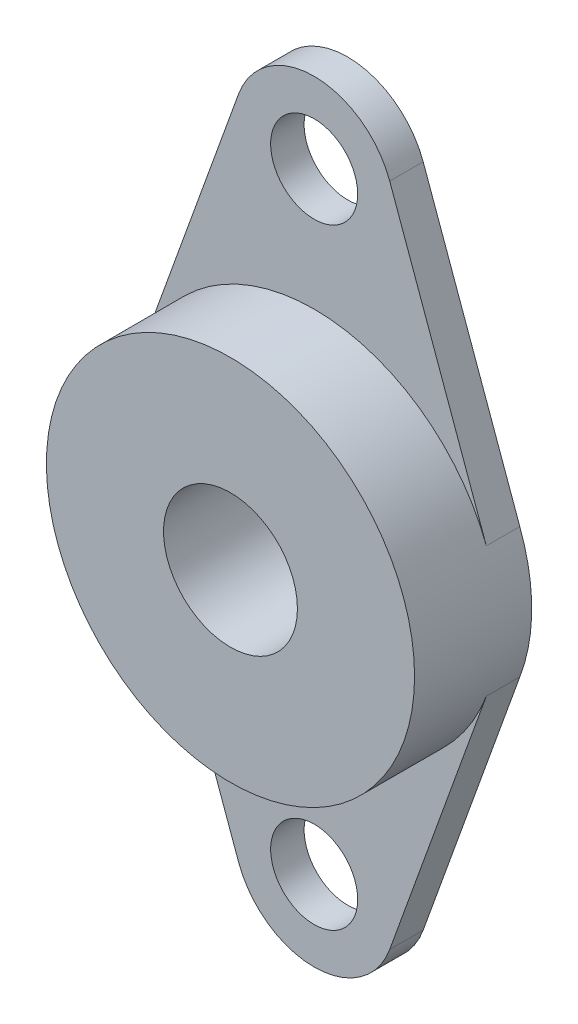
SolidWorks part; units mm, degrees
ref_plane "Alzado" through (0, 0, 0) normal (0, 0, 1) x (1, 0, 0)
ref_plane "Planta" through (0, 0, 0) normal (0, 1, 0) x (1, 0, 0)
ref_plane "Vista lateral" through (0, 0, 0) normal (1, 0, 0) x (0, 0, -1)
sketch "Croquis1" plane through (0, 0, 0) normal (0, 0, 1) x (1, 0, 0)
  line L3 (10.2888, -3.891) -> (4.5146, -19.8804)
  line L5 (-4.5146, -19.8804) -> (-10.2888, -3.891)
  line L6 (-4.5146, 19.8804) -> (-10.2888, 3.891)
  line L7 (4.5146, 19.8804) -> (10.2888, 3.891)
  line L8 (0, 18.25) -> (0, -18.25) construction
  line L9 (-10.2888, 3.891) -> (10.2888, 3.891) construction
  line L10 (10.2888, -3.891) -> (-10.2888, -3.891) construction
  circle A0 centre (0, 0) radius 4
  arc A2 (4.5146, 19.8804) -> (-4.5146, 19.8804) centre (0, 18.25) ccw
  arc A3 (4.5146, -19.8804) -> (-4.5146, -19.8804) centre (0, -18.25) cw
  arc A6 (-10.2888, 3.891) -> (-10.2888, -3.891) centre (0, 0) ccw
  circle A7 centre (0, 18.25) radius 2.6
  circle A8 centre (0, -18.25) radius 2.6
  arc A9 (10.2888, -3.891) -> (10.2888, 3.891) centre (0, 0) ccw
  point P15 (0, 0)
  dimension "D1" = 8
  dimension "D2" = 5.2
  dimension "D3" = 5.2
  dimension "D4" = 22
  dimension "D5" = 4.8
  dimension "D6" = 4.8
  dimension "D7" = 36.5
  dimension "D8" = 17
  dimension "D9" = 17
extrude "Saliente-Extruir1" add sketch "Croquis1" along normal blind 7
sketch "Croquis2" plane through (0, 0, 7) normal (0, 0, 1) x (1, 0, 0)
  line L4 (-10.2888, -3.891) -> (-4.5146, -19.8804)
  line L5 (4.5146, -19.8804) -> (10.2888, -3.891)
  line L6 (10.2888, 3.891) -> (4.5146, 19.8804)
  line L7 (-4.5146, 19.8804) -> (-10.2888, 3.891)
  line L8 (-10.2888, -3.891) -> (-4.5146, -19.8804)
  line L9 (4.5146, -19.8804) -> (10.2888, -3.891)
  line L10 (10.2888, 3.891) -> (4.5146, 19.8804)
  line L11 (-4.5146, 19.8804) -> (-10.2888, 3.891)
  circle A2 centre (0, 0) radius 11
  arc A4 (-10.2888, 3.891) -> (-10.2888, -3.891) centre (0, 0) ccw
  arc A5 (-4.5146, -19.8804) -> (4.5146, -19.8804) centre (0, -18.25) ccw
  arc A6 (10.2888, -3.891) -> (10.2888, 3.891) centre (0, 0) ccw
  arc A7 (4.5146, 19.8804) -> (-4.5146, 19.8804) centre (0, 18.25) ccw
  arc A8 (-10.2888, 3.891) -> (-10.2888, -3.891) centre (0, 0) ccw
  arc A9 (-4.5146, -19.8804) -> (4.5146, -19.8804) centre (0, -18.25) ccw
  arc A10 (10.2888, -3.891) -> (10.2888, 3.891) centre (0, 0) ccw
  arc A11 (4.5146, 19.8804) -> (-4.5146, 19.8804) centre (0, 18.25) ccw
  circle M12 centre (0, -18.25) radius 2.6
  arc M15 (-4.5146, -19.8804) -> (4.5146, -19.8804) centre (0, -18.25) ccw
  line M16 (4.5146, -19.8804) -> (10.2888, -3.891)
  arc M19 (4.5146, 19.8804) -> (-4.5146, 19.8804) centre (0, 18.25) ccw
  line M20 (-4.5146, 19.8804) -> (-10.2888, 3.891)
  circle M22 centre (0, 18.25) radius 2.6
  dimension "D1" = 0
extrude "Cortar-Extruir1" cut sketch "Croquis2" against normal blind 5 contours A2 L10 M19 M20 M22 | A2 L8 M15 M16 M12
